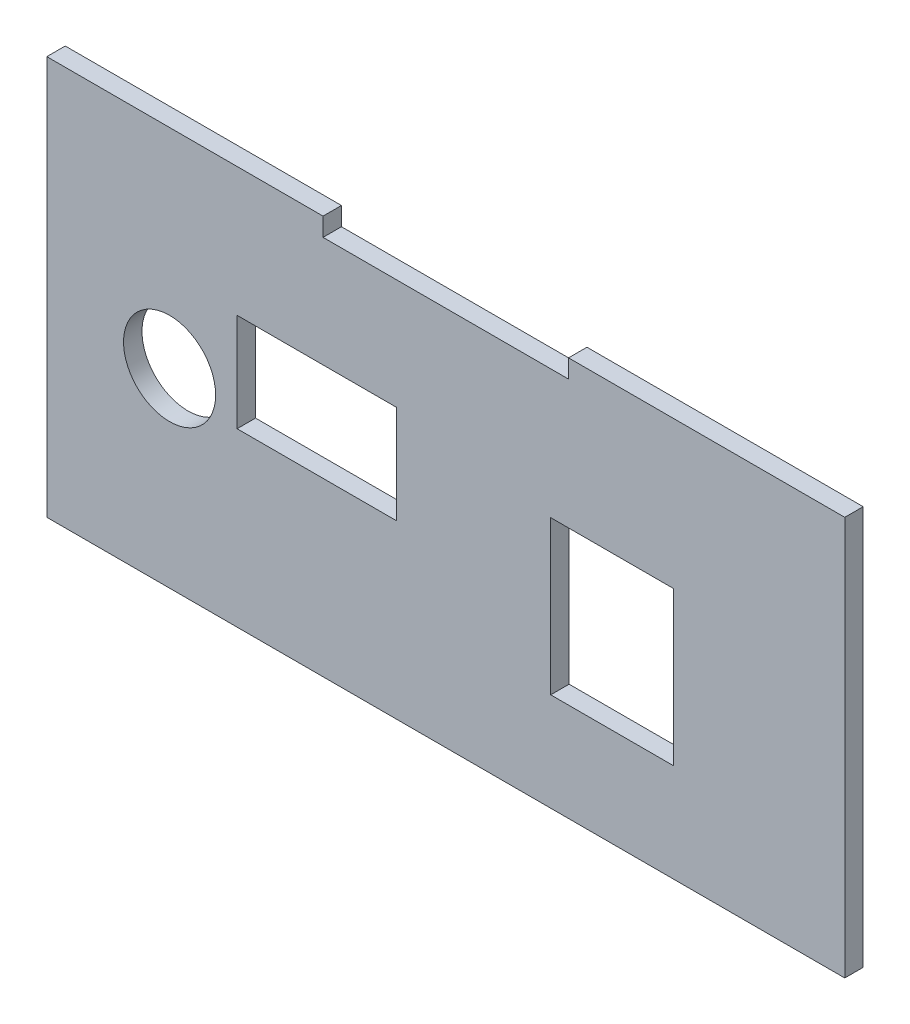
SolidWorks part; units mm, degrees
ref_plane "Plano frontal" through (0, 0, 0) normal (0, 0, 1) x (1, 0, 0)
ref_plane "Plano superior" through (0, 0, 0) normal (0, 1, 0) x (1, 0, 0)
ref_plane "Plano direito" through (0, 0, 0) normal (1, 0, 0) x (0, 0, -1)
sketch "Esboço2" plane through (0, 0, 0) normal (0, 0, 1) x (1, 0, 0)
  line L0 (-95.0471, 49.0441) -> (34.9529, 49.0441)
  line L1 (-95.0471, 49.0441) -> (-95.0471, -15.9559)
  line L2 (-95.0471, -15.9559) -> (34.9529, -15.9559)
  line L3 (34.9529, 49.0441) -> (34.9529, -15.9559)
  line L4 (-50.0471, 49.0441) -> (-10.0471, 49.0441)
  line L5 (-50.0471, 49.0441) -> (-50.0471, 46.0441)
  line L6 (-50.0471, 46.0441) -> (-10.0471, 46.0441)
  line L7 (-10.0471, 49.0441) -> (-10.0471, 46.0441)
  line L8 (-12.9549, 25.0441) -> (7.0451, 25.0441)
  line L9 (-12.9549, 25.0441) -> (-12.9549, 0.0441)
  line L10 (-12.9549, 0.0441) -> (7.0451, 0.0441)
  line L11 (7.0451, 25.0441) -> (7.0451, 0.0441)
  line L13 (-64.0471, 28.0441) -> (-38.0471, 28.0441)
  line L14 (-64.0471, 28.0441) -> (-64.0471, 12.0441)
  line L15 (-64.0471, 12.0441) -> (-38.0471, 12.0441)
  line L16 (-38.0471, 28.0441) -> (-38.0471, 12.0441)
  circle A0 centre (-75.0471, 15.0441) radius 7.5
  dimension "D10" = 15
  dimension "D1" = 45
  dimension "D2" = 0
  dimension "D3" = 130
  dimension "D4" = 40
  dimension "D5" = 45
  dimension "D6" = 3
  dimension "D7" = 41
  dimension "D8" = 25
  dimension "D9" = 31
  dimension "D11" = 20
  dimension "D12" = 65
  dimension "D13" = 11
  dimension "D14" = 16
  dimension "D15" = 26
  dimension "D16" = 28
extrude "Ressalto-extrusão1" add sketch "Esboço2" against normal blind 3 contours L0 L7 L6 L5 L1 L2 L3 A0 L8 L11 L10 L9 L13 L16 L15 L14
